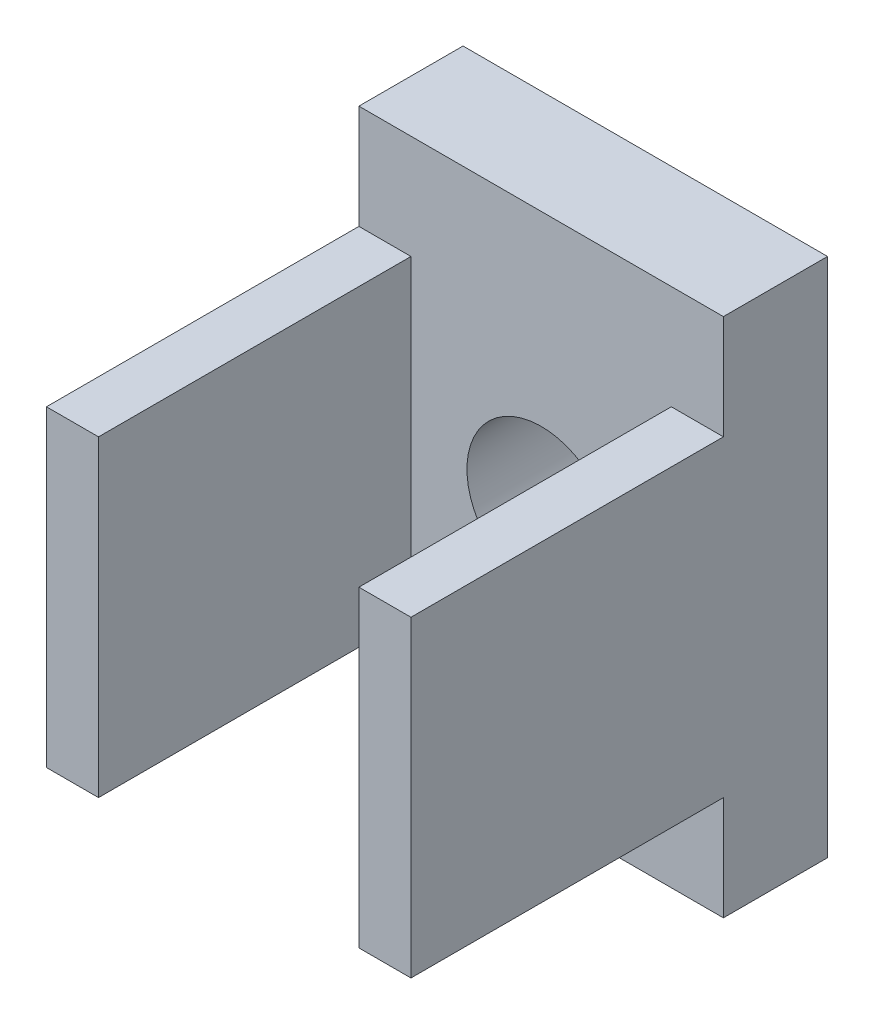
SolidWorks part; units mm, degrees
ref_plane "Front Plane" through (0, 0, 0) normal (0, 0, 1) x (1, 0, 0)
ref_plane "Top Plane" through (0, 0, 0) normal (0, 1, 0) x (1, 0, 0)
ref_plane "Right Plane" through (0, 0, 0) normal (1, 0, 0) x (0, 0, -1)
sketch "Sketch1" plane through (0, 0, 0) normal (0, 0, 1) x (1, 0, 0)
  line L1 (-3.5, 5) -> (3.5, 5)
  line L2 (-3.5, 5) -> (-3.5, -5)
  line L3 (-3.5, -5) -> (3.5, -5)
  line L4 (3.5, 5) -> (3.5, -5)
  line L5 (-3.5, 5) -> (3.5, -5) construction
  line L6 (-3.5, -5) -> (3.5, 5) construction
  point P0 (0, 0)
  dimension "D1" = 10
  dimension "D2" = 7
extrude "Boss-Extrude1" add sketch "Sketch1" along normal blind 2
sketch "Sketch2" plane through (0, 0, 2) normal (0, 0, 1) x (1, 0, 0)
  circle A0 centre (0, 0) radius 1.425
  dimension "D1" = 2.85
extrude "Cut-Extrude1" cut sketch "Sketch2" against normal blind 2
sketch "Sketch3" plane through (0, 0, 2) normal (0, 0, 1) x (1, 0, 0)
  line L0 (-3.5, 3) -> (-2.5, 3)
  line L1 (-3.5, 5) -> (-3.5, -5) construction
  line L2 (-2.5, 3) -> (-2.5, -3)
  line L3 (-2.5, -3) -> (-3.5, -3)
  line L4 (-3.5, -3) -> (-3.5, 3)
  line L5 (3.5, 0) -> (-3.5, 0) construction
  line L6 (3.5, -5) -> (3.5, 5) construction
  line L7 (0, 5) -> (0, -5) construction
  line L8 (3.5, 5) -> (-3.5, 5) construction
  line L9 (-3.5, -5) -> (3.5, -5) construction
  line L10 (2.5, -3) -> (3.5, -3)
  line L11 (2.5, 3) -> (2.5, -3)
  line L12 (3.5, 3) -> (2.5, 3)
  line L13 (3.5, -3) -> (3.5, 3)
  dimension "D1" = 1
  dimension "D2" = 6
extrude "Boss-Extrude2" add sketch "Sketch3" along normal blind 6
